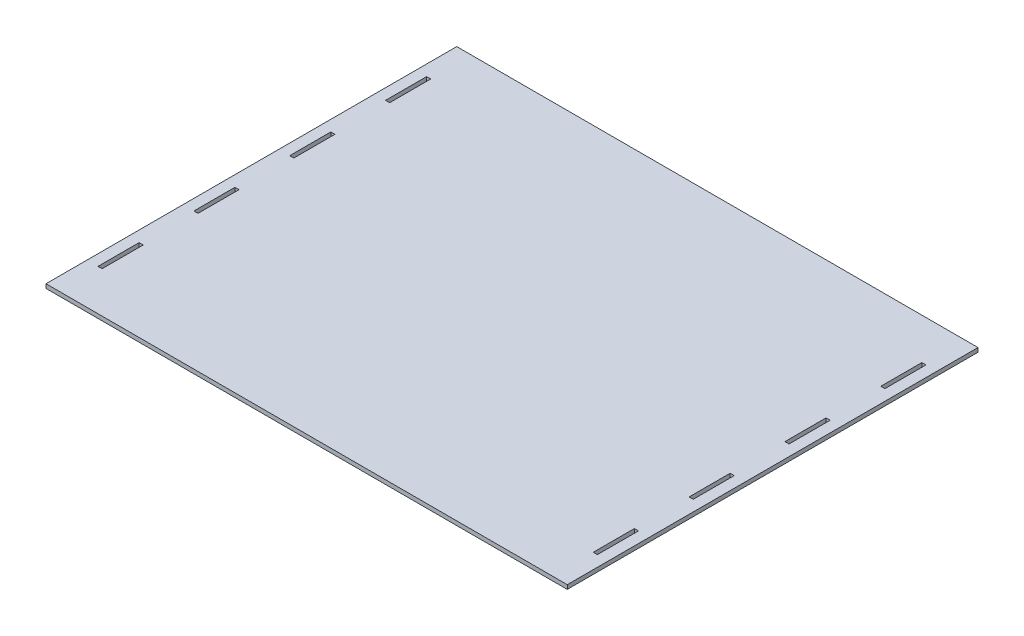
SolidWorks part; units mm, degrees
ref_plane "Front Plane" through (0, 0, 0) normal (0, 0, 1) x (1, 0, 0)
ref_plane "Top Plane" through (0, 0, 0) normal (0, 1, 0) x (1, 0, 0)
ref_plane "Right Plane" through (0, 0, 0) normal (1, 0, 0) x (0, 0, -1)
sketch "Sketch1" plane through (0, 0, 0) normal (0, 1, 0) x (1, 0, 0)
  line L0 (0, 300) -> (380.7157, 300)
  line L1 (0, 300) -> (0, 0)
  line L2 (0, 0) -> (380.7157, 0)
  line L3 (380.7157, 300) -> (380.7157, 0)
  line L4 (7.9957, 270) -> (10.9957, 270)
  line L5 (7.9957, 270) -> (7.9957, 240)
  line L6 (7.9957, 240) -> (10.9957, 240)
  line L7 (10.9957, 270) -> (10.9957, 240)
  line L8 (10.9957, 170) -> (7.9957, 170)
  line L9 (10.9957, 170) -> (10.9957, 200)
  line L10 (10.9957, 200) -> (7.9957, 200)
  line L11 (7.9957, 170) -> (7.9957, 200)
  line L12 (7.9957, 130) -> (10.9957, 130)
  line L13 (7.9957, 130) -> (7.9957, 100)
  line L14 (7.9957, 100) -> (10.9957, 100)
  line L15 (10.9957, 130) -> (10.9957, 100)
  line L16 (7.9957, 60) -> (10.9957, 60)
  line L17 (7.9957, 60) -> (7.9957, 30)
  line L18 (7.9957, 30) -> (10.9957, 30)
  line L19 (10.9957, 60) -> (10.9957, 30)
  line L20 (369.7157, 60) -> (372.7157, 60)
  line L21 (369.7157, 60) -> (369.7157, 30)
  line L22 (369.7157, 30) -> (372.7157, 30)
  line L23 (372.7157, 60) -> (372.7157, 30)
  line L24 (369.7157, 130) -> (372.7157, 130)
  line L25 (369.7157, 130) -> (369.7157, 100)
  line L26 (369.7157, 100) -> (372.7157, 100)
  line L27 (372.7157, 130) -> (372.7157, 100)
  line L28 (369.7157, 200) -> (372.7157, 200)
  line L29 (369.7157, 200) -> (369.7157, 170)
  line L30 (369.7157, 170) -> (372.7157, 170)
  line L31 (372.7157, 200) -> (372.7157, 170)
  line L32 (369.7157, 270) -> (372.7157, 270)
  line L33 (369.7157, 270) -> (369.7157, 240)
  line L34 (369.7157, 240) -> (372.7157, 240)
  line L35 (372.7157, 270) -> (372.7157, 240)
  line L36 (369.7157, 240) -> (369.7157, 200) construction
  line L37 (369.7157, 170) -> (369.7157, 130) construction
  line L38 (369.7157, 100) -> (369.7157, 60) construction
  line L39 (10.9957, 100) -> (10.9957, 60) construction
  line L40 (10.9957, 170) -> (10.9957, 130) construction
  line L41 (10.9957, 240) -> (10.9957, 200) construction
  point P36 (0, 0)
  point P37 (196.0987, -191.3379)
  point P39 (0, 0)
  point P40 (371.2157, 30)
  dimension "D1" = 30
  dimension "D2" = 7.9957
  dimension "D3" = 3
  dimension "D4" = 30
  dimension "D5" = 3
  dimension "D6" = 30
  dimension "D7" = 300
  dimension "D8" = 358.72
  dimension "D9" = 40
  dimension "D10" = 40
  dimension "D11" = 40
  dimension "D12" = 3
  dimension "D13" = 8
  dimension "D14" = 30
  dimension "D15" = 40
  dimension "D16" = 3
  dimension "D17" = 30
  dimension "D18" = 40
  dimension "D19" = 3
  dimension "D20" = 30
  dimension "D21" = 40
  dimension "D22" = 3
  dimension "D23" = 30
  dimension "D24" = 3
  dimension "D25" = 3
  dimension "D26" = 30
  dimension "D27" = 30
  dimension "D28" = 30
extrude "Boss-Extrude1" add sketch "Sketch1" along normal blind 3
